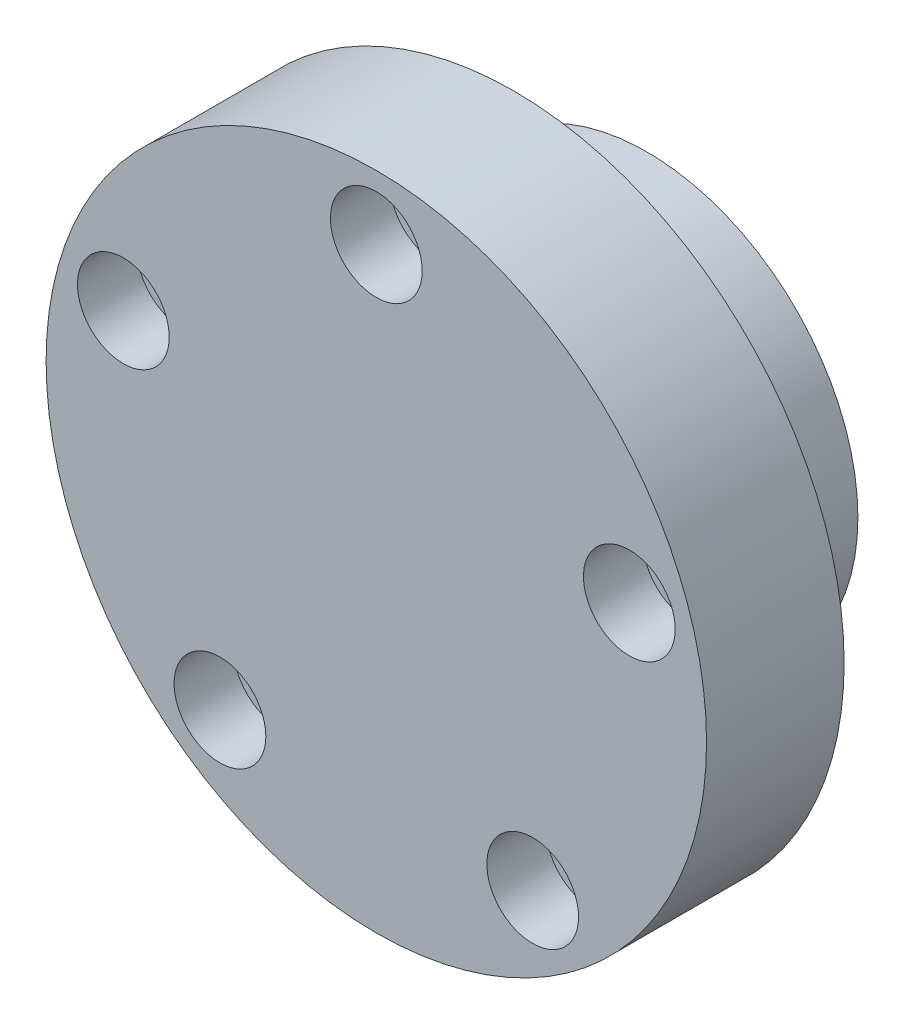
SolidWorks part; units mm, degrees
material "Acrylic (Medium-high impact)"
ref_plane "Front Plane" through (0, 0, 0) normal (0, 0, 1) x (1, 0, 0)
ref_plane "Top Plane" through (0, 0, 0) normal (0, 1, 0) x (1, 0, 0)
ref_plane "Right Plane" through (0, 0, 0) normal (1, 0, 0) x (0, 0, -1)
sketch "Sketch1" plane through (0, 0, 0) normal (0, 0, 1) x (1, 0, 0)
  circle A0 centre (0, 0) radius 18
  dimension "D1" = 36
extrude "Boss-Extrude1" add sketch "Sketch1" along normal blind 7.5
sketch "Sketch2" plane through (0, 0, 0) normal (0, 0, -1) x (-1, 0, 0)
  circle A0 centre (0, 0) radius 11.5
  circle A1 centre (0, 0) radius 4.5
  dimension "D1" = 23
  dimension "D2" = 9
extrude "Boss-Extrude2" add sketch "Sketch2" along normal blind 7.25
sketch "Sketch3" plane through (0, 0, 7.5) normal (0, 0, 1) x (1, 0, 0)
  line L0 (0, 14.5) -> (0, 0) construction
  line L1 (0, 0) -> (13.7903, 4.4807) construction
  line L3 (8.5229, -11.7307) -> (0, 0) construction
  line L4 (0, 0) -> (-8.5229, -11.7307) construction
  line L6 (-13.7903, 4.4807) -> (0, 0) construction
  circle A0 centre (0, 0) radius 14.5 construction
  circle A1 centre (0, 14.5) radius 1.524
  circle A2 centre (13.7903, 4.4807) radius 1.524
  circle A3 centre (8.5229, -11.7307) radius 1.524
  circle A4 centre (-8.5229, -11.7307) radius 1.524
  circle A5 centre (-13.7903, 4.4807) radius 1.524
  dimension "D1" = 29
  dimension "D6" = 3.048
  dimension "D2" = 72
  dimension "D3" = 72
  dimension "D4" = 72
  dimension "D5" = 72
extrude "Cut-Extrude1" cut sketch "Sketch3" against normal blind 16.75
sketch "Sketch4" plane through (0, 0, 7.5) normal (0, 0, 1) x (1, 0, 0)
  circle A0 centre (0, 14.5) radius 2.5
  circle A1 centre (13.7903, 4.4807) radius 2.5
  circle A2 centre (8.5229, -11.7307) radius 2.5
  circle A3 centre (-8.5229, -11.7307) radius 2.5
  circle A4 centre (-13.7903, 4.4807) radius 2.5
  dimension "D1" = 5
extrude "Cut-Extrude2" cut sketch "Sketch4" against normal blind 3.25
